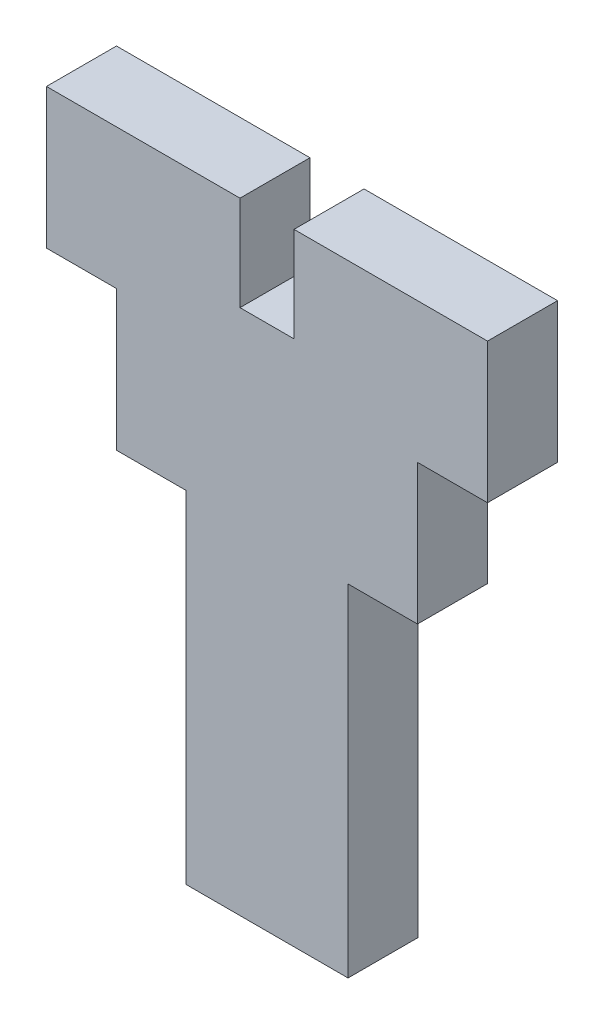
SolidWorks part; units mm, degrees
material "Acrylic (Medium-high impact)"
ref_plane "Front Plane" through (0, 0, 0) normal (0, 0, 1) x (1, 0, 0)
ref_plane "Top Plane" through (0, 0, 0) normal (0, 1, 0) x (1, 0, 0)
ref_plane "Right Plane" through (0, 0, 0) normal (1, 0, 0) x (0, 0, -1)
sketch "Sketch2" plane through (0, 0, 0) normal (0, 0, 1) x (1, 0, 0)
  line L1 (-20, -6.35) -> (20, -6.35)
  line L2 (-20, -6.35) -> (-20, 6.35)
  line L3 (-20, 6.35) -> (20, 6.35)
  line L4 (20, -6.35) -> (20, 6.35)
  line L5 (-20, -6.35) -> (20, 6.35) construction
  line L6 (-20, 6.35) -> (20, -6.35) construction
  point P0 (0, 0)
  dimension "D1" = 12.7
  dimension "D2" = 40
extrude "Boss-Extrude1" add sketch "Sketch2" along normal blind 6.35
sketch "Sketch3" plane through (0, -6.35, 0) normal (0, -1, 0) x (1, 0, 0)
  line L0 (-20, 6.35) -> (20, 6.35) construction
  line L1 (-13.65, 0) -> (13.65, 0)
  line L2 (-13.65, 0) -> (-13.65, 6.35)
  line L3 (-13.65, 6.35) -> (13.65, 6.35)
  line L4 (13.65, 0) -> (13.65, 6.35)
  line L5 (-13.65, 0) -> (13.65, 6.35) construction
  line L6 (-13.65, 6.35) -> (13.65, 0) construction
  line L7 (-20, 0) -> (20, 0) construction
  line L8 (20, 6.35) -> (20, 0) construction
  line L9 (-20, 6.35) -> (-20, 0) construction
  point P0 (0, 3.175)
  dimension "D1" = 0
  dimension "D2" = 0
  dimension "D3" = 6.35
  dimension "D4" = 6.35
extrude "Boss-Extrude2" add sketch "Sketch3" along normal blind 12.7
sketch "Sketch4" plane through (0, 6.35, 0) normal (0, 1, 0) x (1, 0, 0)
  line L0 (20, 0) -> (-20, 0) construction
  line L1 (-2.45, -6.35) -> (2.45, -6.35)
  line L2 (-2.45, -6.35) -> (-2.45, 0)
  line L3 (-2.45, 0) -> (2.45, 0)
  line L4 (2.45, -6.35) -> (2.45, 0)
  line L5 (-2.45, -6.35) -> (2.45, 0) construction
  line L6 (-2.45, 0) -> (2.45, -6.35) construction
  line L7 (20, -6.35) -> (-20, -6.35) construction
  line L8 (20, -6.35) -> (20, 0) construction
  point P0 (0, -3.175)
  dimension "D1" = 0
  dimension "D2" = 0
  dimension "D3" = 4.9
  dimension "D4" = 20
extrude "Cut-Extrude1" cut sketch "Sketch4" against normal blind 8.6
sketch "Sketch5" plane through (0, -19.05, 0) normal (0, -1, 0) x (1, 0, 0)
  line L0 (13.65, 6.35) -> (-13.65, 6.35) construction
  line L1 (-7.35, 0) -> (7.35, 0)
  line L2 (-7.35, 0) -> (-7.35, 6.35)
  line L3 (-7.35, 6.35) -> (7.35, 6.35)
  line L4 (7.35, 0) -> (7.35, 6.35)
  line L5 (-7.35, 0) -> (7.35, 6.35) construction
  line L6 (-7.35, 6.35) -> (7.35, 0) construction
  line L7 (-13.65, 0) -> (13.65, 0) construction
  line L8 (20, 6.35) -> (20, 0) construction
  point P0 (0, 3.175)
  dimension "D1" = 0
  dimension "D2" = 0
  dimension "D3" = 14.7
  dimension "D4" = 20
extrude "Boss-Extrude3" add sketch "Sketch5" along normal blind 30.95
